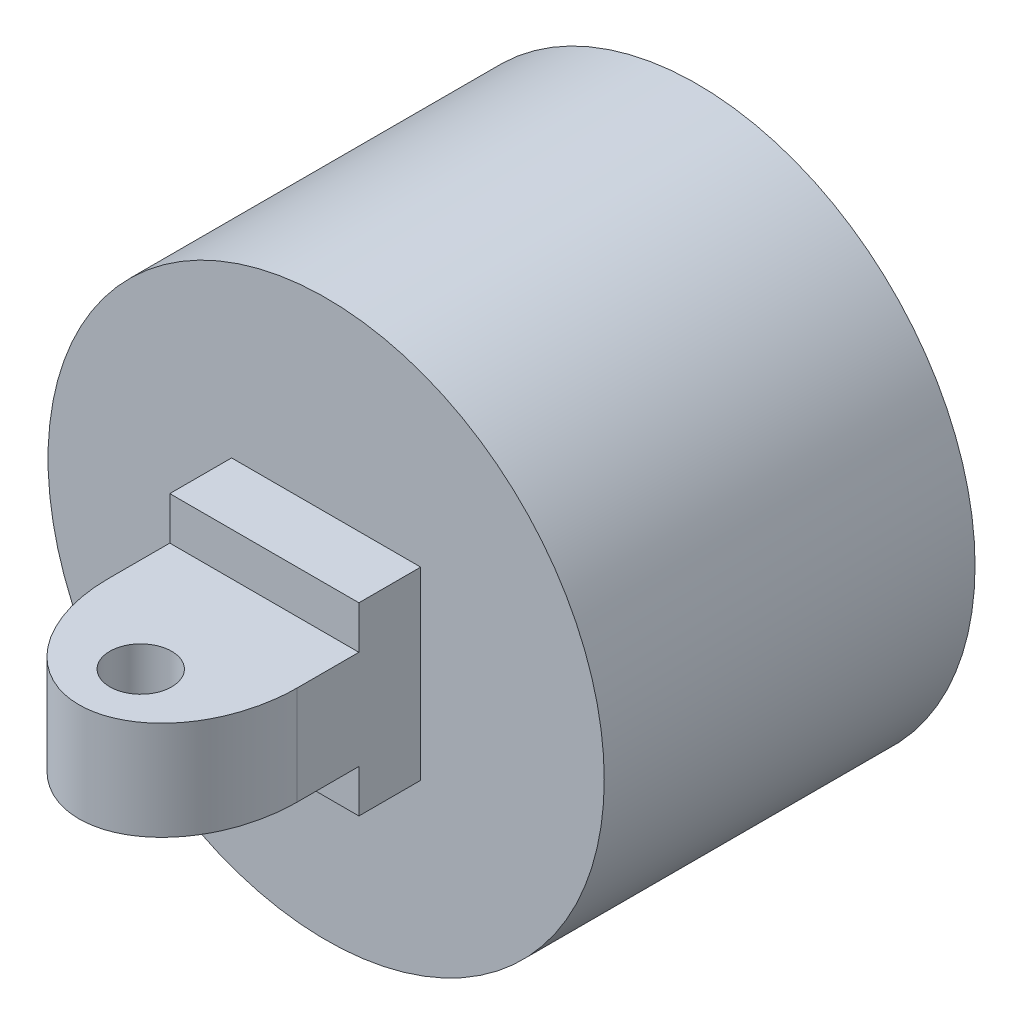
SolidWorks part; units mm, degrees
ref_plane "Front Plane" through (0, 0, 0) normal (0, 0, 1) x (1, 0, 0)
ref_plane "Top Plane" through (0, 0, 0) normal (0, 1, 0) x (1, 0, 0)
ref_plane "Right Plane" through (0, 0, 0) normal (1, 0, 0) x (0, 0, -1)
sketch "Sketch1" plane through (0, 0, 0) normal (0, 0, 1) x (1, 0, 0)
  circle A0 centre (0, 0) radius 22.5
  dimension "D1" = 45
extrude "Boss-Extrude1" add sketch "Sketch1" along normal blind 30
sketch "Sketch2" plane through (0, 0, 0) normal (0, 0, -1) x (-1, 0, 0)
  line L0 (-1.5, -15) -> (1.5, -15)
  line L1 (15, -1.5) -> (-15, -1.5)
  line L2 (15, -1.5) -> (15, 1.5)
  line L3 (15, 1.5) -> (-15, 1.5)
  line L4 (-15, -1.5) -> (-15, 1.5)
  line L5 (15, -1.5) -> (-15, 1.5) construction
  line L6 (15, 1.5) -> (-15, -1.5) construction
  line L7 (-1.5, -15) -> (-1.5, 15)
  line L8 (-1.5, 15) -> (1.5, 15)
  line L9 (1.5, -15) -> (1.5, 15)
  line L10 (-15, 1.5) -> (-15, -1.5)
  line L11 (-15, 1.5) -> (15, 1.5)
  line L12 (15, 1.5) -> (15, -1.5)
  line L13 (-15, -1.5) -> (15, -1.5)
  line L14 (1.5, 15) -> (-1.5, 15)
  line L15 (1.5, 15) -> (1.5, -15)
  line L16 (1.5, -15) -> (-1.5, -15)
  line L17 (-1.5, 15) -> (-1.5, -15)
  circle A0 centre (0, 0) radius 7.5
  point P22 (0, 0)
  dimension "D1" = 15
  dimension "D2" = 30
  dimension "D3" = 3
  dimension "D5" = 15
  dimension "D6" = 15.0748
  dimension "D4" = 4
extrude "Cut-Extrude1" cut sketch "Sketch2" against normal blind 10 contours A0 L15 L8 L17 | L9 A0 L7 L3 | L7 A0 L3 | L11 A0 L9 | L1 A0 L17 | L15 A0 L13
sketch "Sketch3" plane through (0, 0, 30) normal (0, 0, 1) x (1, 0, 0)
  line L1 (7.6498, -7.4691) -> (-7.6498, -7.4691)
  line L2 (7.6498, -7.4691) -> (7.6498, 7.4691)
  line L3 (7.6498, 7.4691) -> (-7.6498, 7.4691)
  line L4 (-7.6498, -7.4691) -> (-7.6498, 7.4691)
  line L5 (7.6498, -7.4691) -> (-7.6498, 7.4691) construction
  line L6 (7.6498, 7.4691) -> (-7.6498, -7.4691) construction
  point P0 (0, 0)
extrude "Boss-Extrude2" add sketch "Sketch3" along normal blind 20
sketch "Sketch4" plane through (-7.6498, 0, 0) normal (-1, 0, 0) x (0, 0, 1)
  line L0 (50, 0) -> (30, 0) construction
  line L1 (50, 7.4691) -> (50, -7.4691) construction
  line L2 (30, 7.4691) -> (30, -7.4691) construction
  line L4 (40, 4) -> (50, 4)
  line L5 (50, 4) -> (50, 0)
  line L6 (50, 0) -> (50, -4)
  line L7 (50, -4) -> (40, -4)
  line L8 (40, -4) -> (35, -4)
  line L9 (35, -4) -> (35, 4)
  line L10 (35, 4) -> (40, 4)
  dimension "D1" = 10
  dimension "D2" = 5
  dimension "D3" = 8
  dimension "D4" = 10
  dimension "D5" = 4
extrude "Cut-Extrude2" cut sketch "Sketch4" against normal blind 20
sketch "Sketch5" plane through (0, 7.4691, 0) normal (0, 1, 0) x (1, 0, 0)
  line L1 (0, -50) -> (0, -30) construction
  line L2 (7.6498, -50) -> (-7.6498, -50) construction
  line L3 (7.6498, -30) -> (-7.6498, -30) construction
  line L4 (0, -40) -> (7.6498, -40) construction
  line L5 (7.6498, -50) -> (7.6498, -30) construction
  line L6 (3.8249, -40) -> (3.8249, -50) construction
  line L7 (3.8249, -45) -> (0, -45) construction
  line L8 (3.8249, -45) -> (7.6498, -45) construction
  line L9 (7.6498, -40) -> (7.6498, -50)
  line L10 (7.6498, -50) -> (0, -50)
  line L11 (0, -50) -> (-7.6498, -50)
  line L12 (-7.6498, -50) -> (-7.6498, -40)
  circle A0 centre (0, -45) radius 2.5
  ellipse E0 centre (0, -40) end of major axis (0, -30) minor radius 7.6498 (-7.6498, -40) -> (7.6498, -40) ccw
  line M4 (-7.6498, -30) -> (-7.6498, -50)
  line M5 (-7.6498, -50) -> (7.6498, -50)
  line M6 (7.6498, -50) -> (7.6498, -30)
  dimension "D1" = 5
extrude "Cut-Extrude4" cut sketch "Sketch5" against normal blind 20 contours A0 | E0 M5 M6 | E0 M4 M5
sketch "Sketch8" plane through (0, -4, 0) normal (0, 1, 0) x (1, 0, 0)
sketch "Sketch10" plane through (0, 7.4691, 0) normal (0, 1, 0) x (1, 0, 0)
  line L0 (-7.6498, -40) -> (7.6498, -40)
  line L1 (0, -40) -> (0, -50) construction
  line L2 (-7.6498, -35) -> (-7.6498, -40)
  line L3 (-7.6498, -40) -> (-7.6498, -30) construction
  line L4 (7.6498, -40) -> (7.6498, -35)
  line L5 (7.6498, -40) -> (7.6498, -30) construction
  line L6 (7.6498, -35) -> (-7.6498, -35)
  ellipse E0 centre (0, -40) end of major axis (0, -50) minor radius 7.6498 (-7.6498, -40) -> (7.6498, -40) ccw
  ellipse E1 centre (0, -40) end of major axis (0, -30) minor radius 7.6498 (-7.6498, -40) -> (7.6498, -40) ccw construction
  circle M2 centre (0, -45) radius 2.5
  line M3 (-7.6498, -30) -> (-7.6498, -40)
  ellipse M4 centre (0, -40) end of major axis (0, -30) minor radius 7.6498 (-7.6498, -40) -> (7.6498, -40) ccw
  line M5 (7.6498, -40) -> (7.6498, -30)
extrude "Cut-Extrude5" cut sketch "Sketch10" against normal blind 11.4 and the other way blind 23 contours L6 L0 M5 M3 | L1 L0 M4 M2 | L0 L1 E0 M2
sketch "Sketch11" plane through (0, -4, 0) normal (0, 1, 0) x (1, 0, 0)
  line L0 (-7.6498, -35) -> (-7.6498, -40)
  line L1 (-7.6498, -40) -> (7.6498, -40)
  line L2 (7.6498, -40) -> (7.6498, -35)
  line L3 (7.6498, -35) -> (-7.6498, -35)
  line L4 (0, -40) -> (0, -50) construction
  circle A0 centre (0, -45) radius 2.5
  ellipse E0 centre (0, -40) end of major axis (0, -30) minor radius 7.6498 (-7.6498, -40) -> (7.6498, -40) ccw construction
  ellipse E1 centre (0, -40) end of major axis (0, -50) minor radius 7.6498 (-7.6498, -40) -> (7.6498, -40) ccw
  circle M7 centre (0, -45) radius 2.5
  line M8 (-7.6498, -35) -> (-7.6498, -40)
  ellipse M9 centre (0, -40) end of major axis (0, -30) minor radius 7.6498 (-7.6498, -40) -> (7.6498, -40) ccw
  line M10 (7.6498, -40) -> (7.6498, -35)
  line M11 (7.6498, -35) -> (-7.6498, -35)
extrude "Boss-Extrude3" add sketch "Sketch11" along normal blind 8 contours L1 M8 M10 M11 | L4 L1 M9 M7 | L1 L4 A0 E1
sketch "Sketch13" plane through (-7.6498, 0, 0) normal (-1, 0, 0) x (0, 0, 1)
  line L0 (50, -7.4691) -> (50, 4) construction
  line L1 (30, -7.4691) -> (50, -7.4691)
  line L2 (30, -7.4691) -> (30, -3.9991)
  line L3 (30, -3.9991) -> (50, -3.9991)
  line L4 (50, -7.4691) -> (50, -3.9991)
  line L5 (35, -3.9991) -> (35, -7.4691)
  line M5 (40, -7.4691) -> (40, 4)
  dimension "D1" = 3.47
extrude "Cut-Extrude6" cut sketch "Sketch13" against normal blind 21 contours L1 L4 L3 M5 | L3 L5 L1 M5
